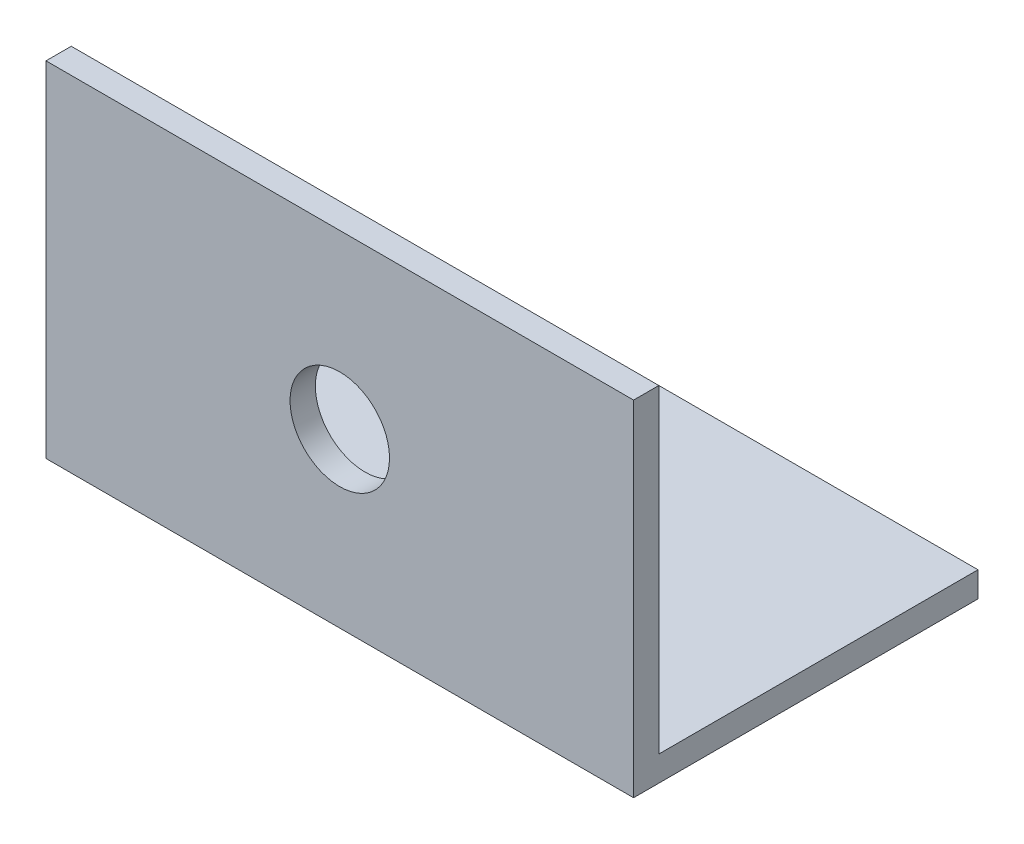
SolidWorks part; units mm, degrees
ref_plane "Front Plane" through (0, 0, 0) normal (0, 0, 1) x (1, 0, 0)
ref_plane "Top Plane" through (0, 0, 0) normal (0, 1, 0) x (1, 0, 0)
ref_plane "Right Plane" through (0, 0, 0) normal (1, 0, 0) x (0, 0, -1)
sketch "Sketch1" plane through (0, 0, 0) normal (1, 0, 0) x (0, 0, -1)
  line L0 (0, 35.306) -> (0, 0)
  line L1 (0, 0) -> (35.306, 0)
  line L2 (35.306, 0) -> (35.306, -2.794)
  line L3 (35.306, -2.794) -> (-2.794, -2.794)
  line L4 (-2.794, -2.794) -> (-2.794, 35.306)
  line L5 (0, 35.306) -> (-2.794, 35.306)
  dimension "D1" = 2.794
  dimension "D2" = 38.1
  dimension "D3" = 38.1
extrude "Boss-Extrude1" add sketch "Sketch1" along normal blind 65
sketch "Sketch2" plane through (0, 0, 2.794) normal (0, 0, 1) x (1, 0, 0)
  line L0 (0, 35.306) -> (0, -2.794) construction
  line L1 (65, -2.794) -> (0, -2.794) construction
  circle A0 centre (32.5, 16.256) radius 5.5
  dimension "D1" = 32.5
  dimension "D2" = 19.05
  dimension "D3" = 11
extrude "Cut-Extrude1" cut sketch "Sketch2" against normal blind 65
